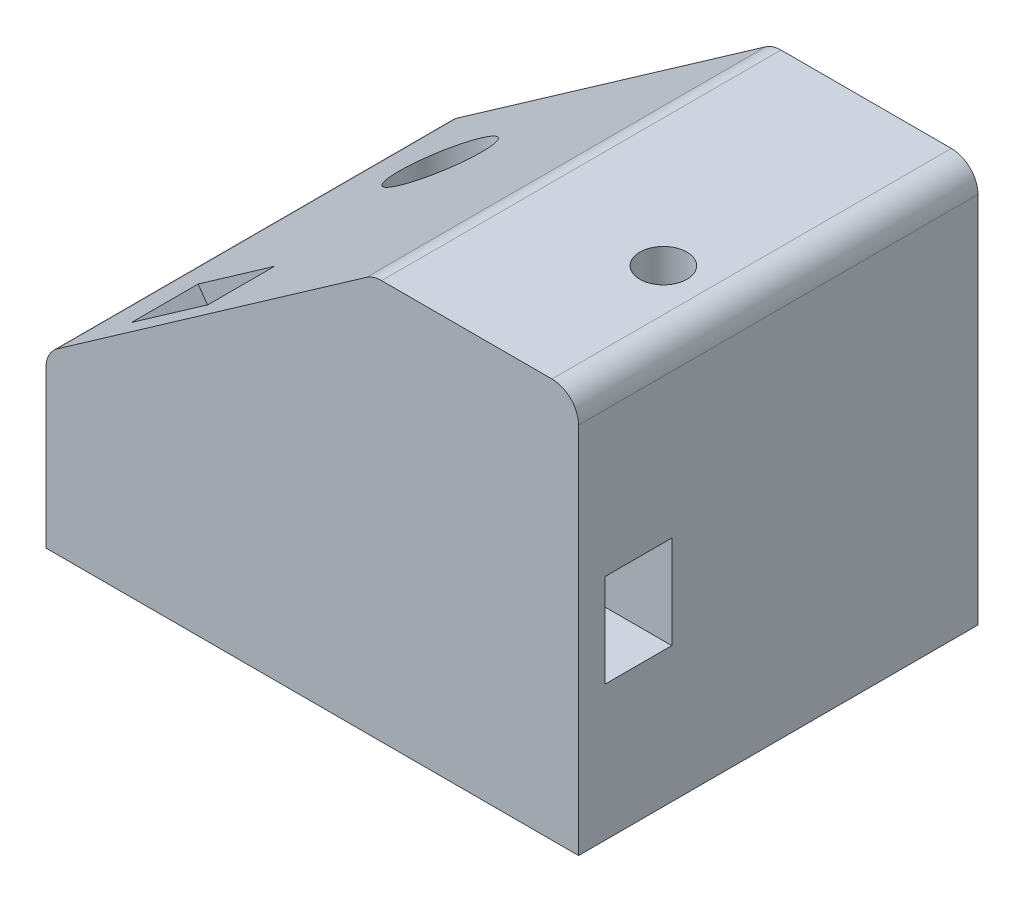
SolidWorks part; units mm, degrees
ref_plane "Front Plane" through (0, 0, 0) normal (0, 0, 1) x (1, 0, 0)
ref_plane "Top Plane" through (0, 0, 0) normal (0, 1, 0) x (1, 0, 0)
ref_plane "Right Plane" through (0, 0, 0) normal (1, 0, 0) x (0, 0, -1)
sketch "Sketch1" plane through (0, 0, 0) normal (0, 0, 1) x (1, 0, 0)
  line L0 (0, 0) -> (50.8, 0)
  line L1 (50.8, 0) -> (50.8, 35.56)
  line L2 (48.26, 38.1) -> (32.0106, 38.1)
  line L3 (30.5537, 37.6406) -> (1.0831, 17.0051)
  line L4 (0, 14.9245) -> (0, 0)
  line L5 (32.0106, 38.1) -> (0, 38.1) construction
  line L6 (0, 0) -> (0, 38.1) construction
  arc A0 (0, 14.9245) -> (1.0831, 17.0051) centre (2.54, 14.9245) cw
  arc A1 (32.0106, 38.1) -> (30.5537, 37.6406) centre (32.0106, 35.56) ccw
  arc A2 (48.26, 38.1) -> (50.8, 35.56) centre (48.26, 35.56) cw
  point P8 (0, 16.2467)
  point P11 (31.2097, 38.1)
  point P14 (50.8, 38.1)
  dimension "D4" = 2.54
  dimension "D1" = 90
  dimension "D2" = 35
  dimension "D3" = 50.8
  dimension "D5" = 38.1
  dimension "D6" = 38.1
  dimension "D7" = 55
extrude "Boss-Extrude1" add sketch "Sketch1" along normal blind 38.1
sketch "Sketch4" plane through (-7.6335, 10.9017, 0) normal (-0.5736, 0.8192, 0) x (0.8192, 0.5736, 0)
  line L0 (16.1803, -29.21) -> (25.0703, -29.21)
  line L1 (25.0703, -29.21) -> (25.0703, -35.56)
  line L2 (25.0703, -35.56) -> (16.1803, -35.56)
  line L3 (16.1803, -35.56) -> (16.1803, -29.21)
  line L4 (8.5603, -38.1) -> (8.5603, 0) construction
  line L5 (46.6179, -38.1) -> (10.641, -38.1) construction
  dimension "D1" = 7.62
  dimension "D2" = 2.54
  dimension "D3" = 8.89
  dimension "D4" = 6.35
extrude "Cut-Extrude1" cut sketch "Sketch4" against normal blind 8.89 contours L1 L2 L3 L0
sketch "Sketch5" plane through (50.8, 0, 0) normal (1, 0, 0) x (0, 0, -1)
  line L2 (-29.21, 12.9001) -> (-35.56, 12.9001)
  line L4 (-29.21, 12.9001) -> (-29.21, 21.7901)
  line L5 (-29.21, 17.9992) -> (-29.21, 25.2815) construction
  line L6 (-29.21, 21.7901) -> (-35.56, 21.7901)
  line L7 (-35.56, 17.9992) -> (-35.56, 25.2815) construction
  line L8 (-35.56, 21.7901) -> (-35.56, 12.9001)
  dimension "D1" = 8.89
extrude "Cut-Extrude2" cut sketch "Sketch5" against normal blind 40.132
sketch "Sketch6" plane through (0, 0, 0) normal (0, -1, 0) x (1, 0, 0)
  line L0 (0, 38.1) -> (50.8, 38.1) construction
  line L1 (50.8, 38.1) -> (50.8, 0) construction
  line L2 (0, 0) -> (50.8, 0) construction
  line L3 (0, 38.1) -> (0, 0) construction
  circle A0 centre (44.2141, 23.4247) radius 2.2479
  circle A2 centre (10.414, 10.922) radius 2.2479
  point P6 (-6.5978, 40.7424)
  point P9 (6.7821, 8.0614)
  dimension "D1" = 14.6753
  dimension "D2" = 4.4958
  dimension "D3" = 6.5859
  dimension "D4" = 10.922
  dimension "D5" = 10.414
extrude "Cut-Extrude3" cut sketch "Sketch6" against normal blind 74.93
sketch "Sketch10" plane through (0, 38.1, 0) normal (0, 1, 0) x (1, 0, 0)
  circle A0 centre (10.414, -10.922) radius 3.937
  dimension "D1" = 7.874
extrude "Cut-Extrude8" cut sketch "Sketch10" against normal blind 11.43 from offset 11.43
